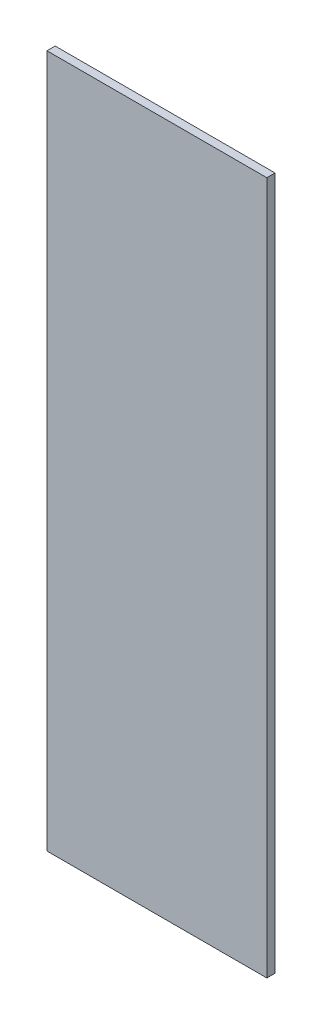
SolidWorks part; units mm, degrees
material "Acrylic (Medium-high impact)"
ref_plane "Front Plane" through (0, 0, 0) normal (0, 0, 1) x (1, 0, 0)
ref_plane "Top Plane" through (0, 0, 0) normal (0, 1, 0) x (1, 0, 0)
ref_plane "Right Plane" through (0, 0, 0) normal (1, 0, 0) x (0, 0, -1)
sketch "Sketch3" plane through (0, 0, 0) normal (0, 0, 1) x (1, 0, 0)
  line L1 (0, 0) -> (-85, 0)
  line L2 (0, 0) -> (0, 267.9)
  line L3 (0, 267.9) -> (-85, 267.9)
  line L4 (-85, 0) -> (-85, 267.9)
  dimension "D1" = 85
  dimension "D2" = 267.9
extrude "Boss-Extrude1" add sketch "Sketch3" along normal blind 3.175
